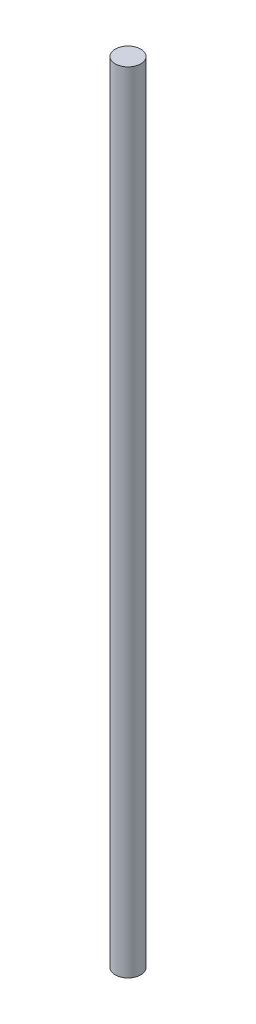
SolidWorks part; units mm, degrees
material "Beech"
ref_plane "Front Plane" through (0, 0, 0) normal (0, 0, 1) x (1, 0, 0)
ref_plane "Top Plane" through (0, 0, 0) normal (0, 1, 0) x (1, 0, 0)
ref_plane "Right Plane" through (0, 0, 0) normal (1, 0, 0) x (0, 0, -1)
sketch "Sketch1" plane through (0, 0, 0) normal (0, 1, 0) x (1, 0, 0)
  circle A0 centre (0, 0) radius 6
  dimension "D1" = 12
extrude "Boss-Extrude1" add sketch "Sketch1" along normal blind 370
